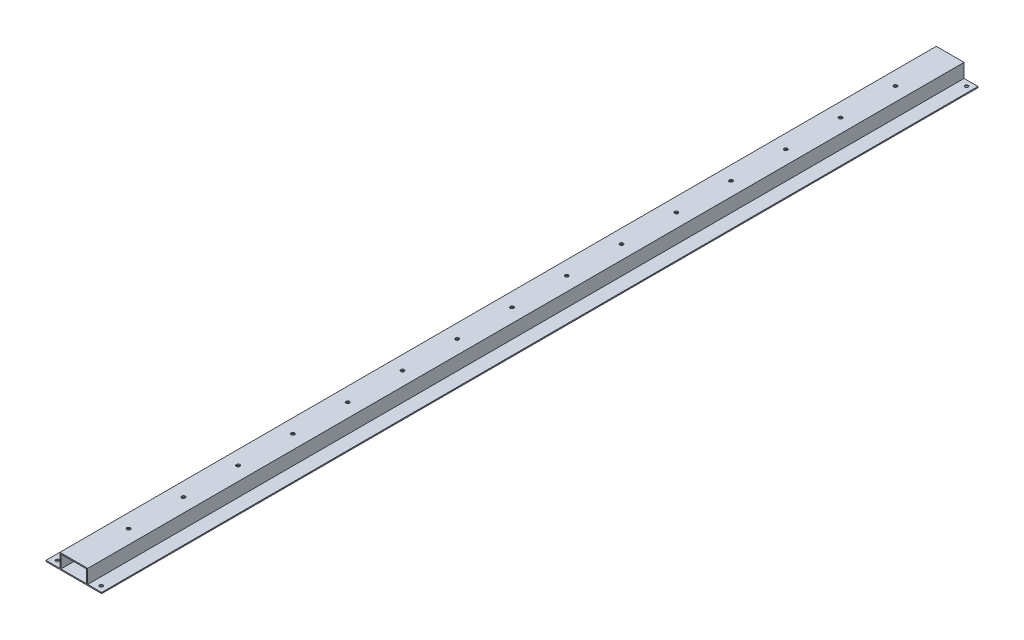
SolidWorks part; units mm, degrees
ref_plane "Alzado" through (0, 0, 0) normal (0, 0, 1) x (1, 0, 0)
ref_plane "Planta" through (0, 0, 0) normal (0, 1, 0) x (1, 0, 0)
ref_plane "Vista lateral" through (0, 0, 0) normal (1, 0, 0) x (0, 0, -1)
sketch "Croquis1" plane through (0, 0, 0) normal (0, 0, 1) x (1, 0, 0)
  line L0 (0, 31.0221) -> (0, -31.113) construction
  line L1 (38.9974, 0) -> (-46.5113, 0) construction
  line L2 (0, 12.7) -> (-11.7, 12.7)
  line L3 (0, 13.7) -> (-12.7, 13.7)
  line L4 (0, 13.7) -> (0, 1) construction
  line L5 (11.7, 1) -> (-11.7, 1)
  line L6 (-12.7, 13.7) -> (-12.7, 1)
  line L7 (25.4, 0) -> (-25.4, 0)
  line L8 (0, 0) -> (0, 1) construction
  line L9 (11.7, 1) -> (-11.7, 1)
  line L10 (-25.4, 0) -> (-25.4, 1)
  line L11 (-11.7, 12.7) -> (-11.7, 1)
  line L12 (-12.7, 1) -> (-25.4, 1)
  line L13 (12.7, 1) -> (25.4, 1)
  line L14 (11.7, 12.7) -> (11.7, 1)
  line L15 (25.4, 0) -> (25.4, 1)
  line L16 (12.7, 13.7) -> (12.7, 1)
  line L17 (0, 13.7) -> (12.7, 13.7)
  line L18 (0, 12.7) -> (11.7, 12.7)
  dimension "D1" = 12.7
  dimension "D2" = 12.7
  dimension "D3" = 1
  dimension "D4" = 1
  dimension "D5" = 25.4
extrude "Saliente-Extruir1" add sketch "Croquis1" along normal mid plane 800 contours L17 L3 L6 L12 L10 L7 L15 L13 L16 L2 L18 L14 L5 L11
sketch "Croquis2" plane through (0, 0, 0) normal (0, -1, 0) x (1, 0, 0)
  line L0 (0, 512.6061) -> (0, -444.1411) construction
  line L1 (-90.5126, 0) -> (85.6051, 0) construction
  line L2 (-20, 395) -> (20, 395) construction
  line L3 (-20, 395) -> (-20, -395) construction
  circle A0 centre (-20, 395) radius 1.5
  circle A1 centre (20, 395) radius 1.5
  circle A2 centre (20, -395) radius 1.5
  circle A3 centre (-20, -395) radius 1.5
  dimension "D2" = 3
  dimension "D1" = 20
  dimension "D3" = 395
  dimension "D6" = 90
  dimension "D7" = 40
  dimension "D8" = 790
  dimension "D4" = 2
  dimension "D5" = 2
extrude "Cortar-Extruir1" cut sketch "Croquis2" against normal blind 10
sketch "Croquis3" plane through (0, 0, 0) normal (0, -1, 0) x (1, 0, 0)
  line L0 (0, 409.8961) -> (0, -499.3596) construction
  line L1 (0, 0) -> (0, 50) construction
  line L2 (0, 0) -> (0, -50) construction
  circle A0 centre (0, 0) radius 1.5875
  circle A1 centre (0, 50) radius 1.5875
  circle A2 centre (0, 100) radius 1.5875
  circle A3 centre (0, 150) radius 1.5875
  circle A4 centre (0, 200) radius 1.5875
  circle A5 centre (0, 250) radius 1.5875
  circle A6 centre (0, 300) radius 1.5875
  circle A7 centre (0, 350) radius 1.5875
  circle A8 centre (0, -50) radius 1.5875
  circle A9 centre (0, -100) radius 1.5875
  circle A10 centre (0, -150) radius 1.5875
  circle A11 centre (0, -200) radius 1.5875
  circle A12 centre (0, -250) radius 1.5875
  circle A13 centre (0, -300) radius 1.5875
  circle A14 centre (0, -350) radius 1.5875
  dimension "D1" = 3.175
  dimension "D3" = 50
  dimension "D5" = 50
  dimension "D2" = 8
  dimension "D4" = 8
extrude "Cortar-Extruir2" cut sketch "Croquis3" against normal through all
